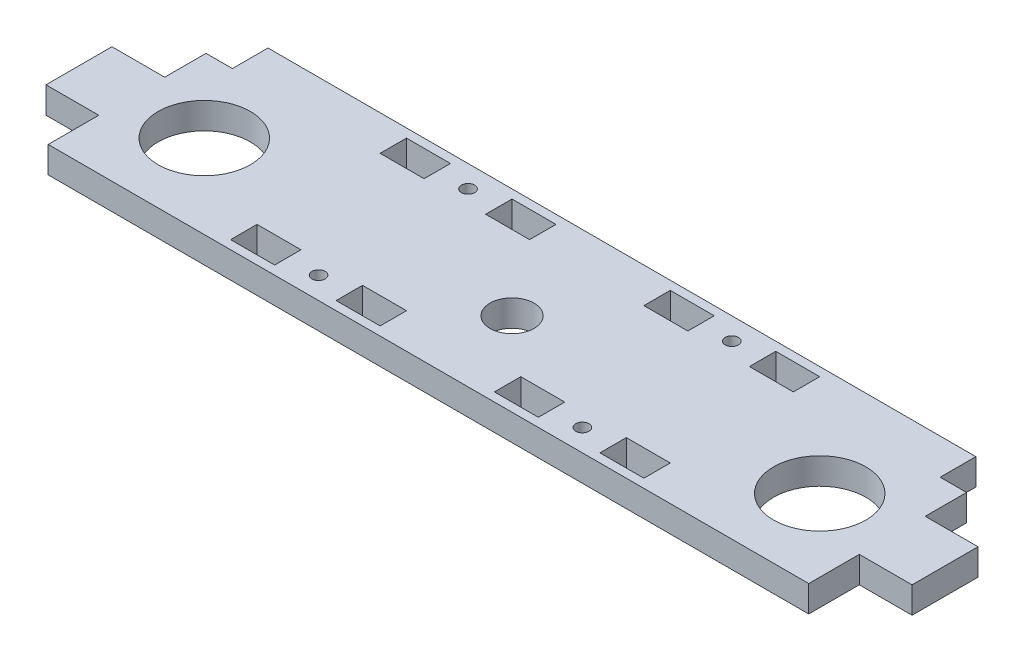
SolidWorks part; units mm, degrees
ref_plane "Спереди" through (0, 0, 0) normal (0, 0, 1) x (1, 0, 0)
ref_plane "Сверху" through (0, 0, 0) normal (0, 1, 0) x (1, 0, 0)
ref_plane "Справа" through (0, 0, 0) normal (1, 0, 0) x (0, 0, -1)
sketch "Эскиз1" plane through (0, 0, 0) normal (0, 1, 0) x (1, 0, 0)
  line L0 (-9.0464, -27.7755) -> (-19.0464, -27.7755)
  line L1 (-9.0464, -21.7755) -> (-9.0464, -27.7755)
  line L2 (-19.0464, -21.7755) -> (-9.0464, -21.7755)
  line L3 (-19.0464, -27.7755) -> (-19.0464, -21.7755)
  line L4 (-43.0464, -27.7755) -> (-43.0464, -21.7755)
  line L5 (-33.0464, -27.7755) -> (-43.0464, -27.7755)
  line L6 (-33.0464, -21.7755) -> (-33.0464, -27.7755)
  line L7 (-43.0464, -21.7755) -> (-33.0464, -21.7755)
  line L8 (-9.0464, 12.2245) -> (-9.0464, 6.2245)
  line L9 (-19.0464, 12.2245) -> (-9.0464, 12.2245)
  line L10 (-19.0464, 6.2245) -> (-19.0464, 12.2245)
  line L11 (-9.0464, 6.2245) -> (-19.0464, 6.2245)
  line L12 (-43.0464, 12.2245) -> (-33.0464, 12.2245)
  line L13 (-43.0464, 6.2245) -> (-43.0464, 12.2245)
  line L14 (-33.0464, 6.2245) -> (-43.0464, 6.2245)
  line L15 (-33.0464, 12.2245) -> (-33.0464, 6.2245)
  line L16 (26.9536, -21.7755) -> (16.9536, -21.7755)
  line L17 (16.9536, -21.7755) -> (16.9536, -27.7755)
  line L18 (16.9536, -27.7755) -> (26.9536, -27.7755)
  line L19 (26.9536, -27.7755) -> (26.9536, -21.7755)
  line L20 (40.9536, -21.7755) -> (40.9536, -27.7755)
  line L21 (40.9536, -27.7755) -> (50.9536, -27.7755)
  line L22 (50.9536, -27.7755) -> (50.9536, -21.7755)
  line L23 (50.9536, -21.7755) -> (40.9536, -21.7755)
  line L24 (90.4536, -29.7755) -> (90.4536, -18.2755)
  line L25 (-82.5464, -29.7755) -> (90.4536, -29.7755)
  line L26 (-82.5464, -29.7755) -> (-82.5464, -18.2755)
  line L27 (-82.5464, -18.2755) -> (-94.5464, -18.2755)
  line L28 (-94.5464, -18.2755) -> (-94.5464, -3.2755)
  line L29 (-94.5464, -3.2755) -> (-82.5464, -3.2755)
  line L30 (-82.5464, -3.2755) -> (-82.5464, 6.1245)
  line L31 (-82.5464, 6.1245) -> (-76.5464, 6.1245)
  line L32 (-76.5464, 6.1245) -> (-76.5464, 14.2245)
  line L33 (84.4536, 14.2245) -> (-76.5464, 14.2245)
  line L34 (84.4536, 6.1245) -> (84.4536, 14.2245)
  line L35 (90.4536, 6.1245) -> (84.4536, 6.1245)
  line L36 (90.4536, -3.2755) -> (90.4536, 6.1245)
  line L37 (102.4536, -3.2755) -> (90.4536, -3.2755)
  line L38 (102.4536, -18.2755) -> (102.4536, -3.2755)
  line L39 (90.4536, -18.2755) -> (102.4536, -18.2755)
  line L40 (26.9536, 6.2245) -> (26.9536, 12.2245)
  line L41 (26.9536, 12.2245) -> (16.9536, 12.2245)
  line L42 (16.9536, 12.2245) -> (16.9536, 6.2245)
  line L43 (16.9536, 6.2245) -> (26.9536, 6.2245)
  line L44 (40.9536, 6.2245) -> (50.9536, 6.2245)
  line L45 (50.9536, 6.2245) -> (50.9536, 12.2245)
  line L46 (50.9536, 12.2245) -> (40.9536, 12.2245)
  line L47 (40.9536, 12.2245) -> (40.9536, 6.2245)
  circle A0 centre (-26.0464, -24.7755) radius 1.5
  circle A1 centre (-66.0464, -10.7755) radius 10.5
  circle A2 centre (-26.0464, 9.2245) radius 1.5
  circle A3 centre (33.9536, -24.7755) radius 1.5
  circle A4 centre (73.9536, -10.7755) radius 10.5
  circle A5 centre (33.9536, 9.2245) radius 1.5
  circle A6 centre (3.9536, -10.7755) radius 5
extrude "Бобышка-Вытянуть1" add sketch "Эскиз1" along normal blind 6
